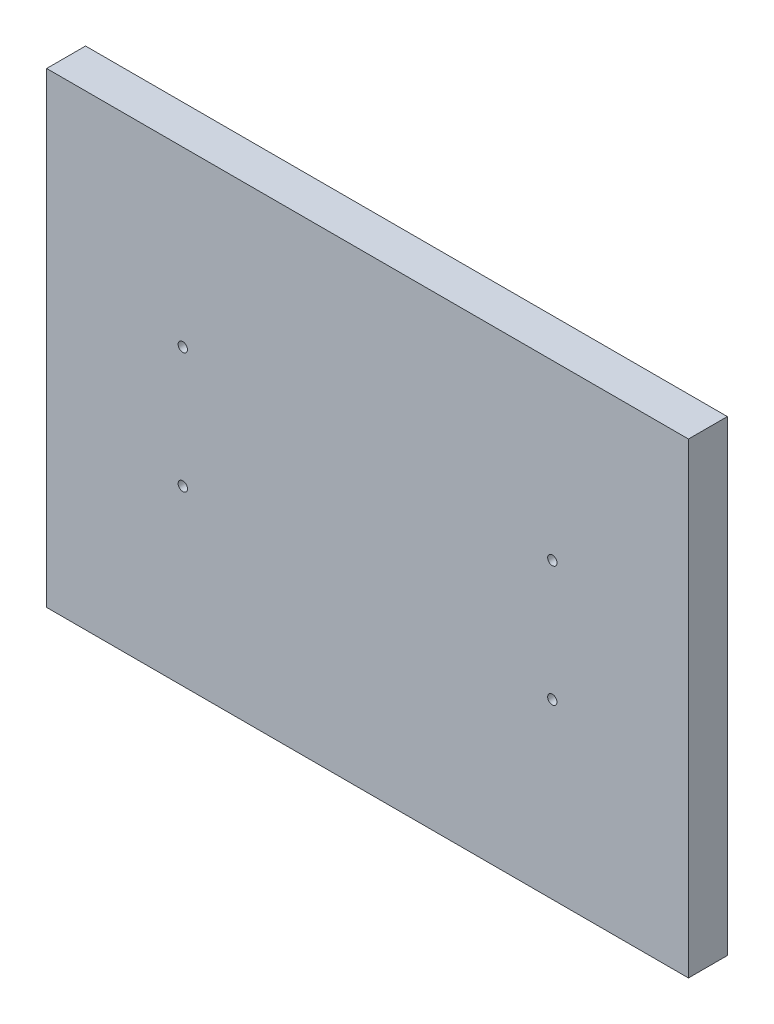
SolidWorks part; units mm, degrees
ref_plane "Ön Düzlem" through (0, 0, 0) normal (0, 0, 1) x (1, 0, 0)
ref_plane "Üst Düzlem" through (0, 0, 0) normal (0, 1, 0) x (1, 0, 0)
ref_plane "Sağ Düzlem" through (0, 0, 0) normal (1, 0, 0) x (0, 0, -1)
sketch "Sketch1" plane through (0, 0, 0) normal (0, 0, 1) x (1, 0, 0)
  line L1 (-82.5, 60) -> (82.5, 60)
  line L2 (-82.5, 60) -> (-82.5, -60)
  line L3 (-82.5, -60) -> (82.5, -60)
  line L4 (82.5, 60) -> (82.5, -60)
  line L5 (-82.5, 60) -> (82.5, -60) construction
  line L6 (-82.5, -60) -> (82.5, 60) construction
  circle A4 centre (-47.5, 15.5) radius 1.2
  circle A5 centre (-47.5, -15.5) radius 1.2
  circle A6 centre (47.5, -15.5) radius 1.2
  circle A7 centre (47.5, 15.5) radius 1.2
  point P0 (0, 0)
  dimension "D3" = 2.4
  dimension "D6" = 44.5
  dimension "D7" = 35
  dimension "D1" = 165
  dimension "D2" = 120
  dimension "D4" = 95
  dimension "D5" = 31
extrude "Boss-Extrude1" add sketch "Sketch1" along normal blind 10
